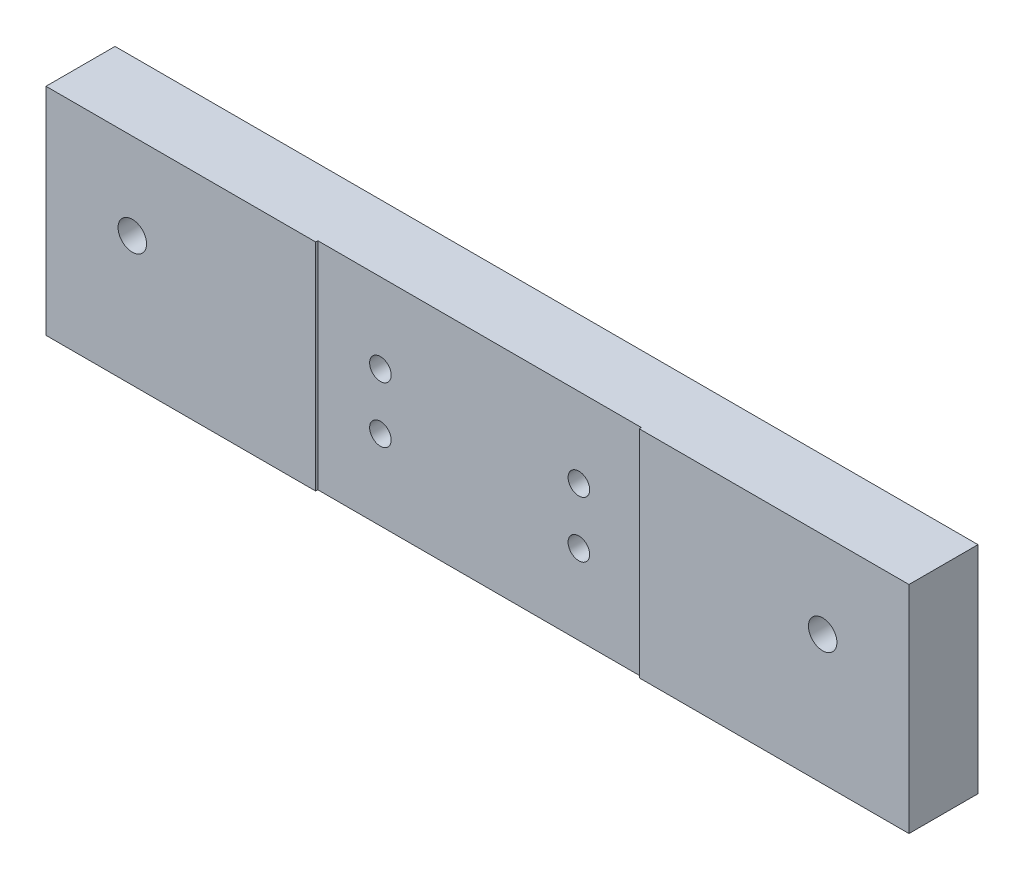
SolidWorks part; units mm, degrees
material "1023 Листовая углеродистая сталь (SS)"
ref_plane "Front" through (0, 0, 0) normal (0, 0, 1) x (1, 0, 0)
ref_plane "Top" through (0, 0, 0) normal (0, 1, 0) x (1, 0, 0)
ref_plane "Right" through (0, 0, 0) normal (1, 0, 0) x (0, 0, -1)
sketch "Sketch1" plane through (0, 0, 0) normal (0, 0, 1) x (1, 0, 0)
  line L1 (-100, 25) -> (100, 25)
  line L2 (-100, 25) -> (-100, -25)
  line L3 (-100, -25) -> (100, -25)
  line L4 (100, 25) -> (100, -25)
  line L5 (-100, 25) -> (100, -25) construction
  line L6 (-100, -25) -> (100, 25) construction
  point P0 (0, 0)
  dimension "D1" = 50
  dimension "D2" = 200
extrude "Extrude1" add sketch "Sketch1" along normal blind 16
sketch "Sketch2" plane through (0, 0, 16) normal (0, 0, 1) x (1, 0, 0)
  line L1 (-37.5, 25) -> (37.5, 25)
  line L2 (-37.5, 25) -> (-37.5, -25)
  line L3 (-37.5, -25) -> (37.5, -25)
  line L4 (37.5, 25) -> (37.5, -25)
  line L5 (-37.5, 25) -> (37.5, -25) construction
  line L6 (-37.5, -25) -> (37.5, 25) construction
  point P0 (0, 0)
  dimension "D1" = 50
  dimension "D2" = 75
extrude "Extrude2" cut sketch "Sketch2" against normal blind 0.5
hole_wizard "M6 Tapped Hole1" positions "Sketch3" profile "Sketch4" tap size "M6" standard "DIN" end condition through all
sketch "Sketch3" plane through (0, 0, 15.5) normal (0, 0, 1) x (1, 0, 0)
  point P0 (-23, 6.5)
  point P3 (-23, -6.5)
  point P6 (23, -6.5)
  point P9 (23, 6.5)
sketch "Sketch4" plane through (-23, 6.5, 15.5) normal (1, 0, 0) x (0, -1, 0)
  line L0 (0, 0) -> (0, 15.5)
  line L1 (0, 15.5) -> (2.5, 15.5)
  line L2 (2.5, 15.5) -> (2.5, 0)
  line L5 (2.5, 0) -> (0, 0)
  line L11 (0, -6.35) -> (0, 107.95) construction
  dimension "Диаметр проходного сверла" = 5
  dimension "Глубина проходного сверла" = 15.5
cosmetic thread "Cosmetic Thread1"
cosmetic thread "Cosmetic Thread2"
cosmetic thread "Cosmetic Thread3"
cosmetic thread "Cosmetic Thread4"
hole_wizard "CBORE for M6 Hex Socket Head Cap Screw1" positions "Sketch5" profile "Sketch6" counterbore size "M6" standard "DIN" end condition through all
sketch "Sketch5" plane through (0, 0, 0) normal (0, 0, -1) x (-1, 0, 0)
  line L1 (-80, 5) -> (80, 5) construction
  line L3 (-100, 25) -> (100, 25) construction
  point P0 (-80, 5)
  point P2 (80, 5)
  dimension "D1" = 20
sketch "Sketch6" plane through (80, 5, 0) normal (1, 0, 0) x (0, 1, 0)
  line L0 (0, 0) -> (0, 16)
  line L1 (0, 16) -> (3.3, 16)
  line L3 (3.3, 16) -> (3.3, 6.4)
  line L4 (3.3, 6.4) -> (5.5, 6.4)
  line L5 (5.5, 6.4) -> (5.5, 0)
  line L7 (5.5, 0) -> (0, 0)
  line L11 (0, -6.35) -> (0, 107.95) construction
  dimension "Диаметр сквозного отверстия" = 6.6
  dimension "Глубина сквозного отверстия" = 16
  dimension "Диаметр цековки" = 11
  dimension "Глубина цековки" = 6.4
